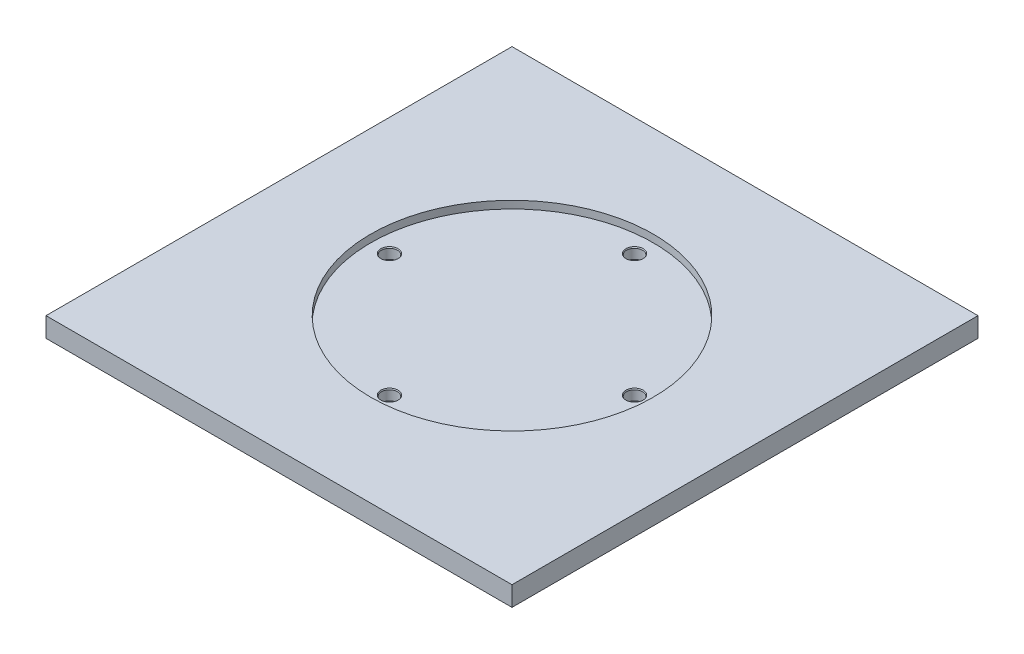
SolidWorks part; units mm, degrees
ref_plane "Front Plane" through (0, 0, 0) normal (0, 0, 1) x (1, 0, 0)
ref_plane "Top Plane" through (0, 0, 0) normal (0, 1, 0) x (1, 0, 0)
ref_plane "Right Plane" through (0, 0, 0) normal (1, 0, 0) x (0, 0, -1)
sketch "Sketch1" plane through (0, 0, 0) normal (0, 1, 0) x (1, 0, 0)
  line L1 (-77, -77) -> (77, -77)
  line L2 (-77, -77) -> (-77, 77)
  line L3 (-77, 77) -> (77, 77)
  line L4 (77, -77) -> (77, 77)
  line L5 (-77, -77) -> (77, 77) construction
  line L6 (-77, 77) -> (77, -77) construction
  point P0 (0, 0)
  dimension "D1" = 154
  dimension "D2" = 154
extrude "Boss-Extrude1" add sketch "Sketch1" along normal blind 6.5
sketch "Sketch2" plane through (0, 6.5, 0) normal (0, 1, 0) x (1, 0, 0)
  circle A0 centre (0, 0) radius 46.7
  dimension "D1" = 93.4
extrude "Cut-Extrude1" cut sketch "Sketch2" against normal blind 2.5
sketch "Sketch3" plane through (0, 4, 0) normal (0, 1, 0) x (1, 0, 0)
  circle A0 centre (0, 0) radius 40.5 construction
  circle A1 centre (0, 40.5) radius 2.65
  circle A2 centre (-40.5, 0) radius 2.65
  circle A3 centre (0, -40.5) radius 2.65
  circle A4 centre (40.5, 0) radius 2.65
  dimension "D1" = 81
  dimension "D2" = 5.3
  dimension "D3" = 5.3
  dimension "D4" = 5.3
  dimension "D5" = 5.3
extrude "Cut-Extrude2" cut sketch "Sketch3" against normal blind 3.5
chamfer "Chamfer1" distance 0.2 angle 60 4 edges at (-40.5, 4, 2.65) (0, 4, 43.15) (0, 4, -37.85) (40.5, 4, 2.65)
